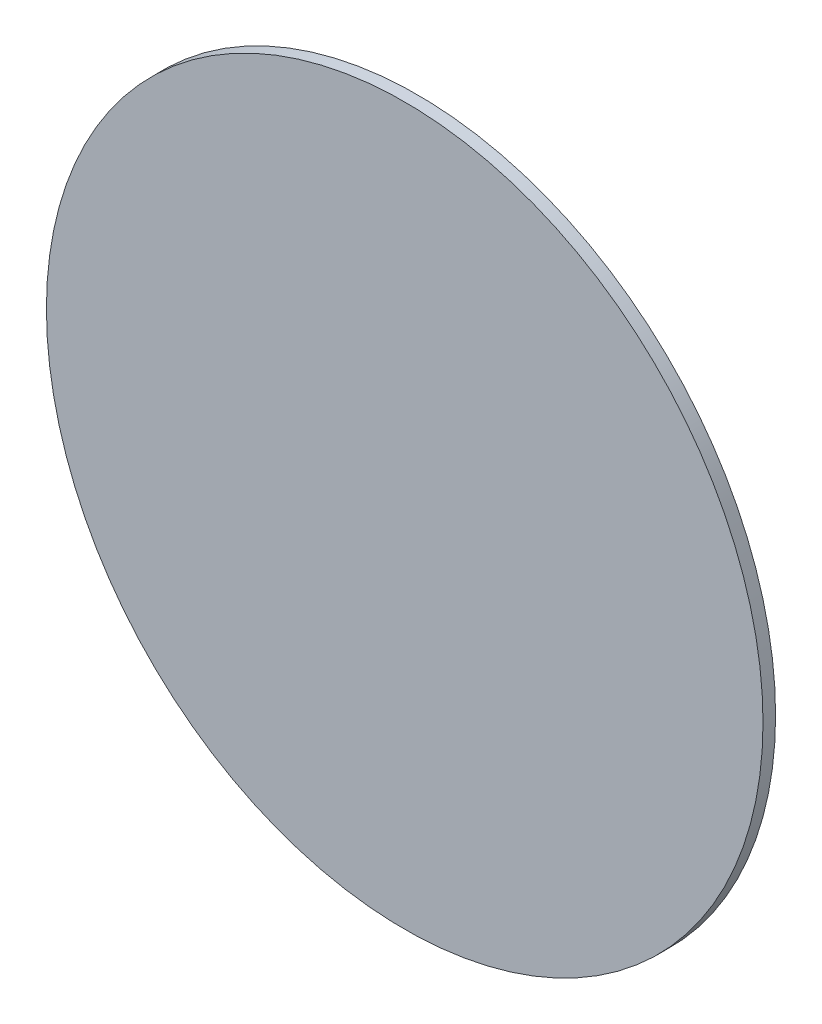
SolidWorks part; units mm, degrees
ref_plane "Plano frontal" through (0, 0, 0) normal (0, 0, 1) x (1, 0, 0)
ref_plane "Plano superior" through (0, 0, 0) normal (0, 1, 0) x (1, 0, 0)
ref_plane "Plano direito" through (0, 0, 0) normal (1, 0, 0) x (0, 0, -1)
sketch "Esboço1" plane through (0, 0, 0) normal (0, 0, 1) x (1, 0, 0)
  circle A0 centre (0, 0) radius 28.5
  dimension "D1" = 57
extrude "Ressalto-extrusão1" add sketch "Esboço1" along normal blind 1
